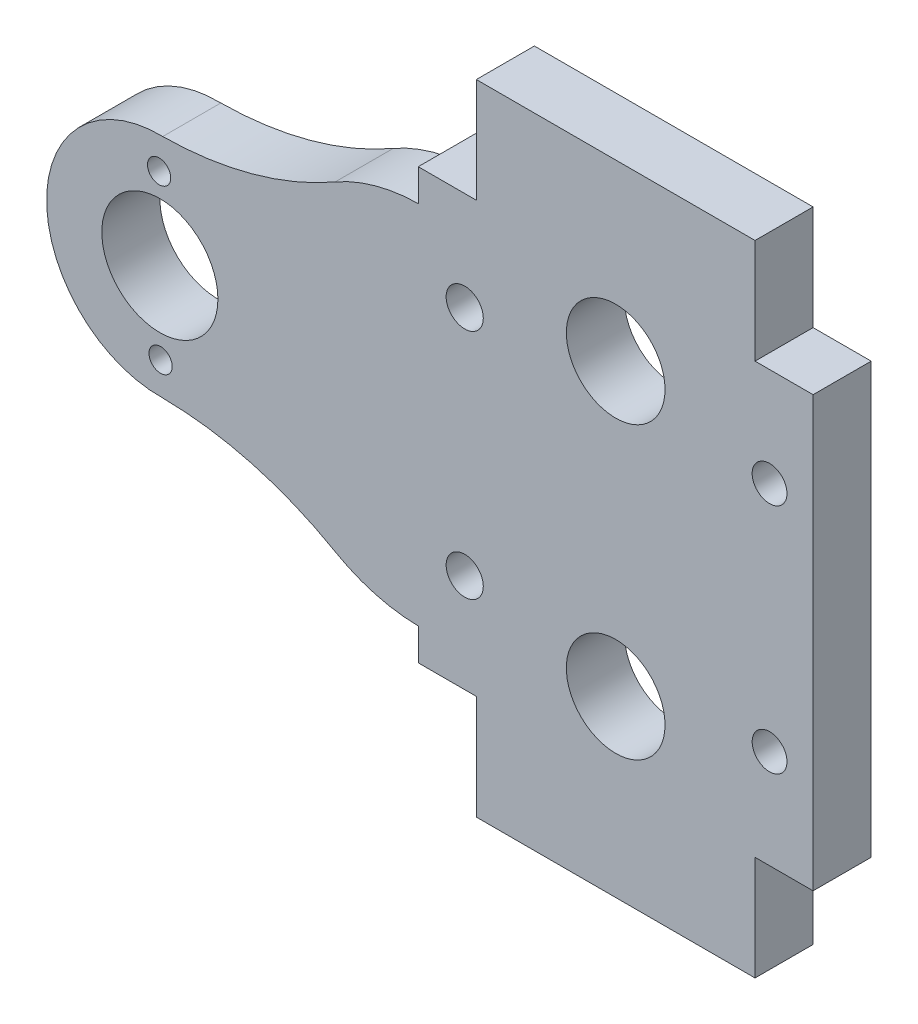
SolidWorks part; units mm, degrees
ref_plane "Front Plane" through (0, 0, 0) normal (0, 0, 1) x (1, 0, 0)
ref_plane "Top Plane" through (0, 0, 0) normal (0, 1, 0) x (1, 0, 0)
ref_plane "Right Plane" through (0, 0, 0) normal (1, 0, 0) x (0, 0, -1)
sketch "Sketch1" plane through (0, 0, 0) normal (0, 0, 1) x (1, 0, 0)
  line L30 (45.2509, -25.2077) -> (50.0009, -20.4577)
  line L31 (50.0009, -20.4577) -> (50.0009, 24.6887)
  line L32 (50.0009, 24.6887) -> (45.1474, 29.5423)
  line L33 (45.1474, 29.5423) -> (26.3545, 29.5423)
  line L34 (26.3545, 29.5423) -> (21.2509, 24.4387)
  line L35 (21.2509, 24.4387) -> (21.2509, 18.0423)
  line L36 (21.2509, 18.0423) -> (20.4081, 18.0423)
  line L37 (20.4081, 18.0423) -> (16.7009, 18.0423)
  line L38 (-5.4991, 12.0433) -> (-5.4991, 12.0391)
  line L39 (-5.4991, -7.4545) -> (-5.4991, -7.4587)
  line L40 (16.7009, -13.4577) -> (20.4081, -13.4577)
  line L41 (20.4081, -13.4577) -> (21.2509, -13.4577)
  line L42 (21.2509, -13.4577) -> (21.2509, -20.2077)
  line L43 (21.2509, -20.2077) -> (26.2509, -25.2077)
  line L44 (26.2509, -25.2077) -> (45.2509, -25.2077)
  arc A10 (16.7009, 18.0423) -> (9.3423, 16.0756) centre (16.7009, 3.2923) ccw
  arc A11 (-5.4991, 12.0433) -> (9.3423, 16.0756) centre (-5.7491, 42.2923) ccw
  arc A12 (-5.4991, 12.0391) -> (-5.4991, -7.4545) centre (-5.7491, 2.2923) ccw
  arc A13 (9.3423, -11.491) -> (-5.4991, -7.4587) centre (-5.7491, -37.7077) ccw
  arc A14 (9.3423, -11.491) -> (16.7009, -13.4577) centre (16.7009, 1.2923) ccw
  circle A25 centre (46.7509, -7.7077) radius 1.5
  circle A26 centre (46.7509, 12.2923) radius 1.5
  circle A27 centre (33.5009, 14.7923) radius 4.25
  circle A28 centre (33.5009, -10.2077) radius 4.25
  circle A29 centre (19.2509, 12.2923) radius 1.5
  circle A30 centre (19.2509, -7.7077) radius 1.5
  circle B0 centre (-5.7491, 2.2923) radius 5
  circle B1 centre (1.2509, 2.3547) radius 1
  circle B2 centre (-5.6866, -4.7077) radius 1
  circle B3 centre (-12.7491, 2.2298) radius 1
  circle B4 centre (-5.8115, 9.2923) radius 1
  dimension "D2" = 8.5
  dimension "D3" = 3
  dimension "D4" = 14.75
  dimension "D5" = 30.25
  dimension "D6" = 9.75
  dimension "D8" = 9.3423
  dimension "D9" = 16.7009
  dimension "D10" = 19.2509
  dimension "D11" = 20.4081
  dimension "D12" = 21.2509
  dimension "D13" = 26.2509
  dimension "D14" = 26.3545
  dimension "D15" = 33.5009
  dimension "D16" = 45.1474
  dimension "D17" = 45.2509
  dimension "D18" = 46.7509
  dimension "D19" = 50.0009
  dimension "D20" = 5.4991
  dimension "D22" = 1.2923
  dimension "D26" = 2.2923
  dimension "D28" = 24.4387
  dimension "D30" = 24.6887
  dimension "D31" = 20.2077
  dimension "D32" = 12.2923
  dimension "D33" = 14.7923
  dimension "D43" = 7.7077
  dimension "D44" = 10.2077
sketch_block_instance "Block1-1"
sketch_block "Block1" parameters "D1"=2, "D2"=10
extrude "Boss-Extrude2" add sketch "Sketch1" along normal blind 5
sketch "Sketch2" plane through (0, 0, 0) normal (0, 0, -1) x (-1, 0, 0)
  line L0 (-26.2509, -25.2077) -> (-21.5009, -25.2077)
  line L1 (-21.5009, -25.2077) -> (-21.5009, -20.4577)
  line L2 (-21.5009, -16.2077) -> (-21.5009, -25.2077) construction
  line L3 (-21.2509, -20.2077) -> (-26.2509, -25.2077) construction
  line L4 (-21.5009, -20.4577) -> (-26.2509, -25.2077)
  line L5 (-45.2509, -25.2077) -> (-45.5009, -25.2077)
  line L6 (-45.5009, -25.2077) -> (-45.5009, -24.9577)
  line L7 (-45.2509, -25.2077) -> (-50.0009, -20.4577) construction
  line L8 (-45.5009, -25.2077) -> (-45.5009, -16.2077) construction
  line L9 (-45.5009, -24.9577) -> (-45.2509, -25.2077)
  line L10 (-45.5009, 29.1887) -> (-45.5009, 29.7923)
  line L11 (-50.0009, 24.6887) -> (-45.1474, 29.5423) construction
  line L12 (-45.5009, 20.7923) -> (-45.5009, 29.7923) construction
  line L13 (-45.5009, 29.7923) -> (-21.5009, 29.7923)
  line L14 (-21.5009, 29.7923) -> (-21.5009, 24.6887)
  line L15 (-26.3545, 29.5423) -> (-21.2509, 24.4387) construction
  line L16 (-21.5009, 29.7923) -> (-21.5009, 20.7923) construction
  line L17 (-21.5009, 24.6887) -> (-26.3545, 29.5423)
  line L18 (-26.3545, 29.5423) -> (-45.1474, 29.5423)
  line L19 (-45.1474, 29.5423) -> (-45.5009, 29.1887)
  line L20 (-50.5009, 20.7923) -> (-50.0009, 20.7923)
  line L21 (-50.0009, -20.4577) -> (-50.0009, 24.6887) construction
  line L22 (-50.5009, 20.7923) -> (-45.5009, 20.7923) construction
  line L23 (-50.0009, 20.7923) -> (-50.0009, -16.2077)
  line L24 (-45.5009, -16.2077) -> (-50.5009, -16.2077) construction
  line L25 (-50.0009, -16.2077) -> (-50.5009, -16.2077)
  line L26 (-50.5009, -16.2077) -> (-50.5009, 20.7923)
extrude "Boss-Extrude3" add sketch "Sketch2" against normal up to vertex (5 mm away)
sketch "Sketch3" plane through (0, 0, 0) normal (0, 0, -1) x (-1, 0, 0)
  line L0 (-50.0009, -16.2077) -> (-45.5009, -16.2077)
  line L1 (-45.5009, -16.2077) -> (-45.5009, -25.2077)
  line L2 (-45.5009, -25.2077) -> (-50.0009, -20.4577)
  line L3 (-50.0009, -20.4577) -> (-50.0009, -16.2077)
  line L4 (-50.5009, 20.7923) -> (-45.5009, 20.7923)
  line L5 (-45.5009, 20.7923) -> (-45.5009, 29.1887)
  line L6 (-45.5009, 29.1887) -> (-50.0009, 24.6887)
  line L7 (-50.0009, 24.6887) -> (-50.5009, 20.7923)
  line L8 (-21.5009, -16.2077) -> (-21.5009, -20.4577)
  line L9 (-21.5009, -20.4577) -> (-21.2509, -20.2077)
  line L10 (-21.2509, -20.2077) -> (-21.2509, -16.2077)
  line L11 (-21.2509, -13.4577) -> (-21.2509, -20.2077) construction
  line L12 (-16.5009, -16.2077) -> (-21.5009, -16.2077) construction
  line L13 (-21.2509, -16.2077) -> (-21.5009, -16.2077)
  line L14 (-21.5009, 20.7923) -> (-21.2509, 20.7923)
  line L15 (-21.2509, 24.4387) -> (-21.2509, 18.0423) construction
  line L16 (-21.5009, 20.7923) -> (-16.5009, 20.7923) construction
  line L17 (-21.2509, 20.7923) -> (-21.2509, 24.4387)
  line L18 (-21.2509, 24.4387) -> (-21.5009, 24.6887)
  line L19 (-21.5009, 24.6887) -> (-21.5009, 20.7923)
extrude "Cut-Extrude1" cut sketch "Sketch3" against normal blind 10
sketch "Sketch4" plane through (0, 0, 0) normal (0, 0, -1) x (-1, 0, 0)
  line L0 (-21.2509, 20.7923) -> (-16.5009, 20.7923)
  line L1 (-16.5009, 20.7923) -> (-16.5009, 18.0409)
  line L2 (-16.5009, 20.7923) -> (-16.5009, -16.2077) construction
  line L3 (-21.2509, 20.7923) -> (-21.2509, 18.0423)
  line L4 (-21.2509, 18.0423) -> (-16.7009, 18.0423)
  line L5 (-16.5009, -13.4564) -> (-16.5009, -16.2077)
  line L6 (-16.5009, -16.2077) -> (-21.2509, -16.2077)
  line L7 (-21.2509, -16.2077) -> (-21.2509, -13.4577)
  line L8 (-21.2509, -13.4577) -> (-16.7009, -13.4577)
  arc A0 (-9.3423, 16.0756) -> (-16.7009, 18.0423) centre (-16.7009, 3.2923) ccw construction
  arc A1 (-16.5009, 18.0409) -> (-16.7009, 18.0423) centre (-16.7009, 3.2923) ccw
  arc A2 (-16.7009, -13.4577) -> (-16.5009, -13.4564) centre (-16.7009, 1.2923) ccw
  arc A3 (-16.7009, -13.4577) -> (-9.3423, -11.491) centre (-16.7009, 1.2923) ccw construction
extrude "Boss-Extrude4" add sketch "Sketch4" against normal up to vertex (5 mm away)
sketch "Sketch5" plane through (0, 0, 5) normal (0, 0, 1) x (1, 0, 0)
  circle A0 centre (20.5009, -7.7077) radius 1.6
  circle A1 centre (20.5009, 12.2923) radius 1.6
  circle A2 centre (20.5009, -7.7077) radius 2.1 construction
  circle A3 centre (20.5009, 12.2923) radius 2.1 construction
  dimension "D1" = 3.2
  dimension "D2" = 3.2
extrude "Cut-Extrude2" cut sketch "Sketch5" against normal blind 10
sketch "Sketch6" plane through (0, 0, 5) normal (0, 0, 1) x (1, 0, 0)
  arc A0 (19.7519, -6.2938) -> (19.7519, -9.1216) centre (20.5009, -7.7077) ccw
  arc A1 (19.7519, -6.2938) -> (19.7519, -9.1216) centre (19.2509, -7.7077) ccw
  arc A2 (19.7519, 13.7062) -> (19.7519, 10.8784) centre (20.5009, 12.2923) ccw
  arc A3 (19.7519, 13.7062) -> (19.7519, 10.8784) centre (19.2509, 12.2923) ccw
extrude "Boss-Extrude5" add sketch "Sketch6" against normal up to vertex (5 mm away)
sketch "Sketch7" plane through (0, 0, 0) normal (0, 0, -1) x (-1, 0, 0)
  circle A0 centre (-1.2509, 2.3547) radius 1
  circle A1 centre (12.7491, 2.2298) radius 1
extrude "Boss-Extrude6" add sketch "Sketch7" against normal up to vertex (5 mm away)
